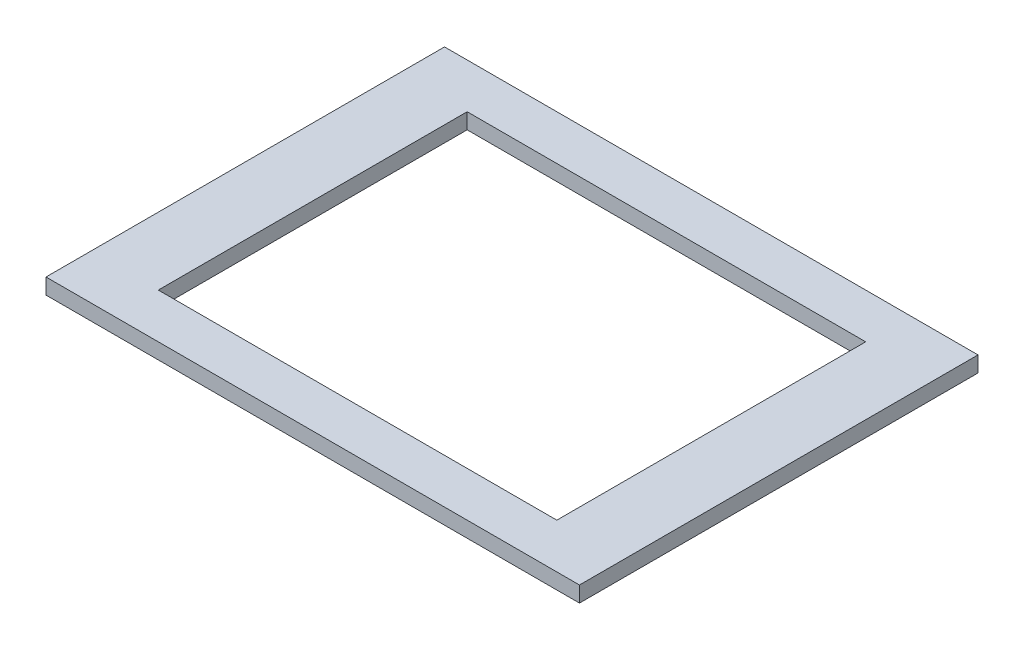
SolidWorks part; units mm, degrees
ref_plane "Front Plane" through (0, 0, 0) normal (0, 0, 1) x (1, 0, 0)
ref_plane "Top Plane" through (0, 0, 0) normal (0, 1, 0) x (1, 0, 0)
ref_plane "Right Plane" through (0, 0, 0) normal (1, 0, 0) x (0, 0, -1)
sketch "Sketch1" plane through (0, 0, 0) normal (0, 1, 0) x (1, 0, 0)
  line L1 (170, -127) -> (-170, -127)
  line L2 (170, -127) -> (170, 127)
  line L3 (170, 127) -> (-170, 127)
  line L4 (-170, -127) -> (-170, 127)
  line L5 (170, -127) -> (-170, 127) construction
  line L6 (170, 127) -> (-170, -127) construction
  point P0 (0, 0)
  dimension "D1" = 254
  dimension "D2" = 340
extrude "Boss-Extrude1" add sketch "Sketch1" along normal mid plane 10
sketch "Sketch2" plane through (0, 5, 0) normal (0, 1, 0) x (1, 0, 0)
  line L1 (127, -98.425) -> (-127, -98.425)
  line L2 (127, -98.425) -> (127, 98.425)
  line L3 (127, 98.425) -> (-127, 98.425)
  line L4 (-127, -98.425) -> (-127, 98.425)
  line L5 (127, -98.425) -> (-127, 98.425) construction
  line L6 (127, 98.425) -> (-127, -98.425) construction
  point P0 (0, 0)
  dimension "D1" = 196.85
  dimension "D2" = 254
extrude "Cut-Extrude1" cut sketch "Sketch2" against normal up to next
